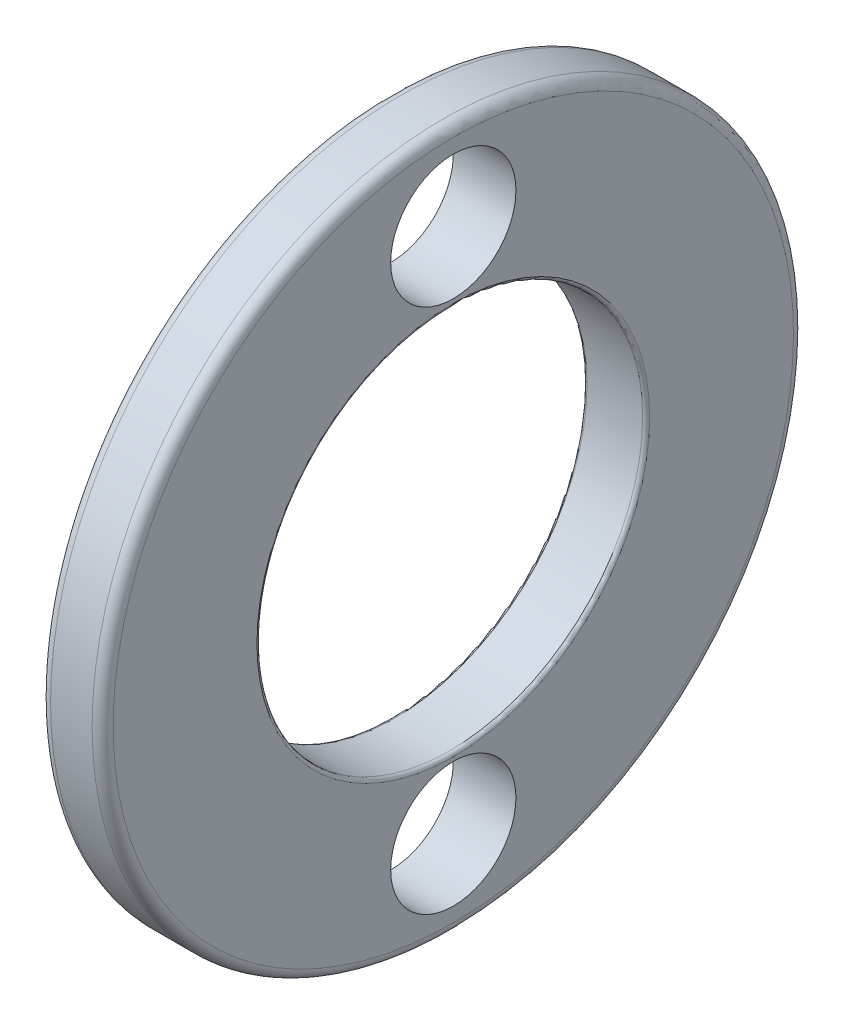
SolidWorks part; units mm, degrees
ref_plane "Alzado" through (0, 0, 0) normal (0, 0, 1) x (1, 0, 0)
ref_plane "Planta" through (0, 0, 0) normal (0, 1, 0) x (1, 0, 0)
ref_plane "Vista lateral" through (0, 0, 0) normal (1, 0, 0) x (0, 0, -1)
ref_plane "Plano1" through (0, 0, 0) normal (0, 0, 1) x (1, 0, 0)
sketch "Croquis1" plane through (0, 0, 0) normal (0, 0, 1) x (1, 0, 0)
  line L0 (5.214, 19.4) -> (5.214, 11.2)
  line L1 (5.414, 11) -> (8.586, 11)
  line L2 (8.786, 11.2) -> (8.786, 19.4)
  line L3 (8.186, 20) -> (5.814, 20)
  line L4 (50, 0) -> (-50, 0) construction
  arc A0 (5.214, 11.2) -> (5.414, 11) centre (5.414, 11.2) ccw
  arc A1 (8.586, 11) -> (8.786, 11.2) centre (8.586, 11.2) ccw
  arc A2 (8.786, 19.4) -> (8.186, 20) centre (8.186, 19.4) ccw
  arc A3 (5.814, 20) -> (5.214, 19.4) centre (5.814, 19.4) ccw
revolve "Revolución1" add sketch "Croquis1" angle 360 about L4
ref_plane "Plano2" through (0, 0, 0) normal (1, 0, 0) x (0, 0, -1)
sketch "Croquis2" plane through (0, 0, 0) normal (1, 0, 0) x (0, 0, -1)
  circle A0 centre (0, 15) radius 3.572
extrude "Extruir1" cut sketch "Croquis2" along normal blind 12.358
ref_plane "Plano3" through (0, 0, 0) normal (1, 0, 0) x (0, 0, -1)
sketch "Croquis3" plane through (0, 0, 0) normal (1, 0, 0) x (0, 0, -1)
  circle A0 centre (0, -15) radius 3.572
extrude "Extruir2" cut sketch "Croquis3" along normal blind 12.358
